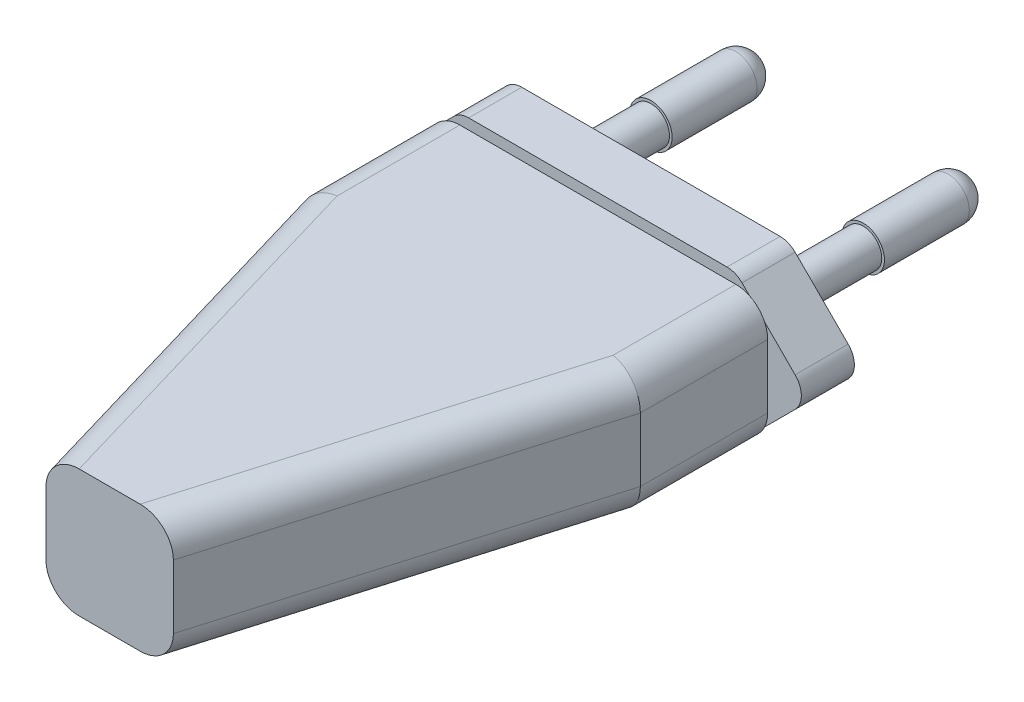
SolidWorks part; units mm, degrees
ref_plane "Front Plane" through (0, 0, 0) normal (0, 0, 1) x (1, 0, 0)
ref_plane "Top Plane" through (0, 0, 0) normal (0, 1, 0) x (1, 0, 0)
ref_plane "Right Plane" through (0, 0, 0) normal (1, 0, 0) x (0, 0, -1)
sketch "Sketch1" plane through (0, 0, 0) normal (0, 1, 0) x (1, 0, 0)
  line L0 (0, -13.0248) -> (0, 61.1697) construction
  line L1 (-6, 0) -> (6, 0)
  line L2 (6, 0) -> (11, 17)
  line L3 (11, 17) -> (16, 34)
  line L4 (16, 34) -> (16, 46)
  line L5 (16, 46) -> (-16, 46)
  line L7 (-6, 0) -> (-11, 17)
  line L8 (-11, 17) -> (-16, 34)
  line L9 (-16, 34) -> (-16, 46)
  point P8 (0, 46)
  dimension "D1" = 6
  dimension "D2" = 16
  dimension "D4" = 17
  dimension "D5" = 17
  dimension "D6" = 12
extrude "Boss-Extrude1" add sketch "Sketch1" along normal blind 12
fillet "Fillet1" radius 3 8 edges at (-11, 0, -17) (-16, 0, -40) (-16, 12, -40) (-11, 12, -17) (11, 0, -17) (16, 0, -40) (16, 12, -40) (11, 12, -17)
sketch "Sketch3" plane through (0, 0, -46) normal (0, 0, -1) x (-1, 0, 0)
  line L0 (-13, 13) -> (13, 13)
  line L1 (13, 13) -> (20, 6)
  line L2 (20, 6) -> (13, -1)
  line L3 (13, -1) -> (-13, -1)
  line L4 (-13, -1) -> (-20, 6)
  line L5 (-20, 6) -> (-13, 13)
  line L6 (-13, 12) -> (-13, -8.0349) construction
  line L7 (13, 12) -> (13, -5.5401) construction
  line L8 (16, 6) -> (-26.4356, 6) construction
  line L9 (16, 9) -> (16, 3) construction
  line L10 (-13, 12) -> (13, 12) construction
  line L12 (-13, 0) -> (13, 0) construction
  point P17 (0, 0)
  point P18 (0, 0)
  point P19 (0, 0)
  point P20 (0, 0)
  point P21 (0, 0)
  point P22 (0, 0)
  point P25 (0, 0)
  dimension "D1" = 1
  dimension "D2" = 1
extrude "Boss-Extrude2" add sketch "Sketch3" along normal blind 5
fillet "Fillet2" radius 2 6 edges at (13, -1, -48.5) (20, 6, -48.5) (13, 13, -48.5) (-13, -1, -48.5) (-13, 13, -48.5) (-20, 6, -48.5)
sketch "Sketch4" plane through (0, 0, -51) normal (0, 0, -1) x (-1, 0, 0)
  line L0 (-19.1716, 6) -> (19.1716, 6) construction
  line L1 (0, 13) -> (0, -1) construction
  line L2 (12.1716, 13) -> (-12.1716, 13) construction
  line L3 (-12.1716, -1) -> (12.1716, -1) construction
  arc A0 (-18.5858, 7.4142) -> (-18.5858, 4.5858) centre (-17.1716, 6) ccw construction
  arc A1 (18.5858, 4.5858) -> (18.5858, 7.4142) centre (17.1716, 6) ccw construction
  circle A2 centre (-10, 6) radius 1.75
  circle A3 centre (10, 6) radius 1.75
  dimension "D1" = 3.5
  dimension "D2" = 10
extrude "Boss-Extrude3" add sketch "Sketch4" along normal blind 10
sketch "Sketch5" plane through (0, 0, -61) normal (0, 0, -1) x (-1, 0, 0)
  circle A0 centre (10, 6) radius 2
  circle A1 centre (-10, 6) radius 2
  dimension "D1" = 4
  dimension "D2" = 4
extrude "Boss-Extrude4" add sketch "Sketch5" along normal blind 10
fillet "Fillet3" radius 2 2 edges at (-12, 6, -71) (8, 6, -71)
